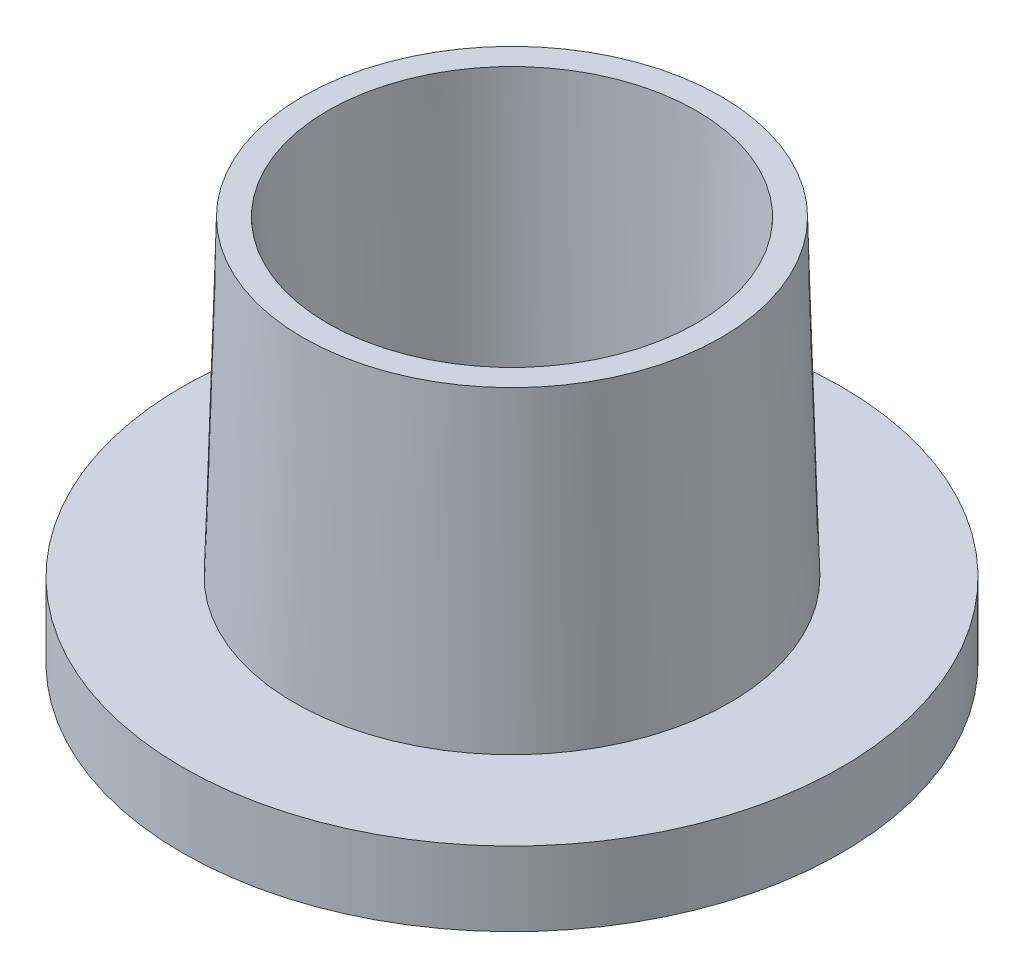
SolidWorks part; units mm, degrees
ref_plane "Front Plane" through (0, 0, 0) normal (0, 0, 1) x (1, 0, 0)
ref_plane "Top Plane" through (0, 0, 0) normal (0, 1, 0) x (1, 0, 0)
ref_plane "Right Plane" through (0, 0, 0) normal (1, 0, 0) x (0, 0, -1)
sketch "Sketch1" plane through (0, 0, 0) normal (0, 0, 1) x (1, 0, 0)
  line L0 (0, 0) -> (0, 120.015) construction
  line L1 (-10.6, 0) -> (-11.185, 23.42)
  line L2 (-11.185, 23.42) -> (-12.685, 23.42)
  line L3 (-12.685, 23.42) -> (-12.1, 0) construction
  line L4 (-12.1, 0) -> (-10.6, 0)
  line L5 (-12.685, 23.42) -> (-13.2127, 4.5)
  line L6 (-13.2127, 4.5) -> (-20, 4.5)
  line L7 (-20, 4.5) -> (-20, 0)
  line L8 (-20, 0) -> (-12.1, 0)
  point P6 (-13.9414, 4.5)
  dimension "D1" = 1.5
  dimension "D2" = 12.1
  dimension "D3" = 11.185
  dimension "D4" = 23.42
  dimension "D5" = 20
  dimension "D6" = 4.5
  dimension "D7" = 1
revolve "Revolve1" add sketch "Sketch1" angle 360 about L0
